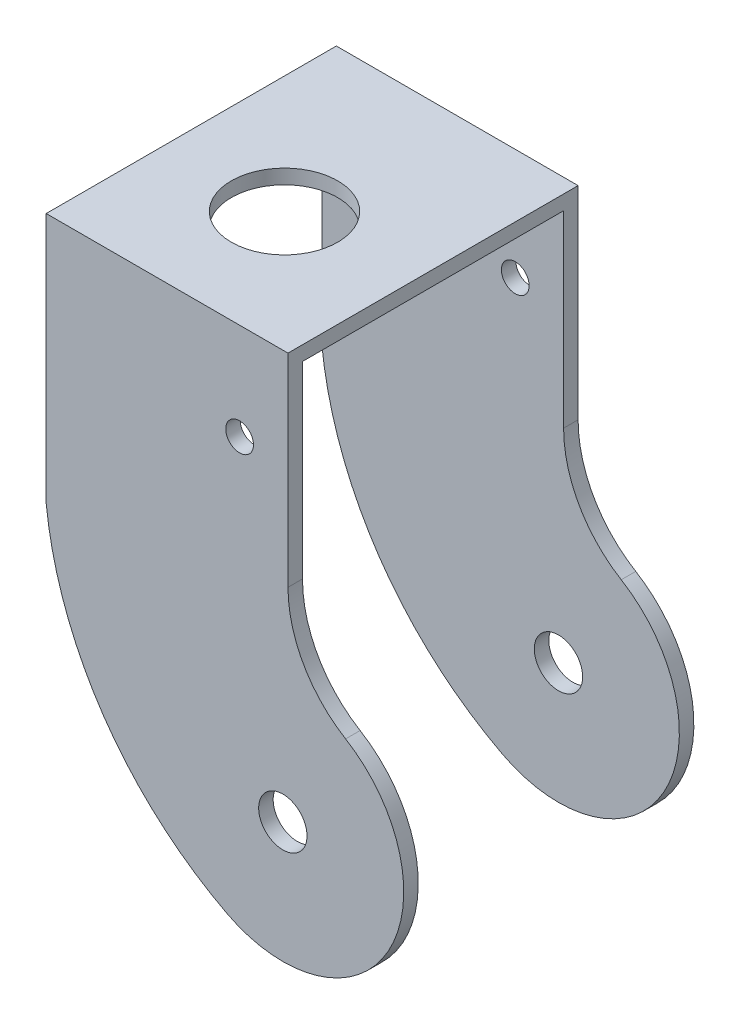
SolidWorks part; units mm, degrees
ref_plane "前视基准面" through (0, 0, 0) normal (0, 0, 1) x (1, 0, 0)
ref_plane "上视基准面" through (0, 0, 0) normal (0, 1, 0) x (1, 0, 0)
ref_plane "右视基准面" through (0, 0, 0) normal (1, 0, 0) x (0, 0, -1)
sketch "草图1" plane through (0, 0, 0) normal (0, 0, 1) x (1, 0, 0)
  line L0 (-24.2815, 46.5644) -> (-24.2815, -5.3788)
  line L1 (-24.2815, 46.5644) -> (25.7185, 46.5644)
  line L2 (25.7185, 46.5644) -> (25.7185, 4.6204)
  arc A0 (-24.2815, -5.3788) -> (13.108, -60.1085) centre (45.5586, 2.1971) ccw
  arc A1 (13.108, -60.1085) -> (37.6385, -16.5706) centre (24.6563, -37.9356) ccw
  arc A2 (25.7185, 4.6204) -> (37.6385, -16.5706) centre (50.515, 4.6204) ccw
  circle A3 centre (24.6563, -37.9356) radius 5
  circle A4 centre (15.7185, 26.5644) radius 2.8703
  dimension "D1" = 10
  dimension "D2" = 20
  dimension "D3" = 10
  dimension "D4" = 84.5
extrude "凸台-拉伸1" add sketch "草图1" along normal blind 60
sketch "草图2" plane through (-24.2815, 0, 0) normal (-1, 0, 0) x (0, 0, 1)
  line L0 (3, 43.5644) -> (3, -96.1228)
  line L1 (3, -96.1228) -> (57, -96.1228)
  line L2 (57, -96.1228) -> (57, 43.5644)
  line L3 (57, 43.5644) -> (3, 43.5644)
  line L4 (0, 46.5644) -> (0, -5.3788) construction
  line L5 (60, 46.5644) -> (0, 46.5644) construction
  dimension "D1" = 54
  dimension "D2" = 3
  dimension "D3" = 3
extrude "切除-拉伸1" cut sketch "草图2" against normal through all
sketch "草图3" plane through (0, 46.5644, 0) normal (0, 1, 0) x (1, 0, 0)
  circle A0 centre (0, -35) radius 11
  dimension "D1" = 22
extrude "切除-拉伸2" cut sketch "草图3" against normal blind 70
